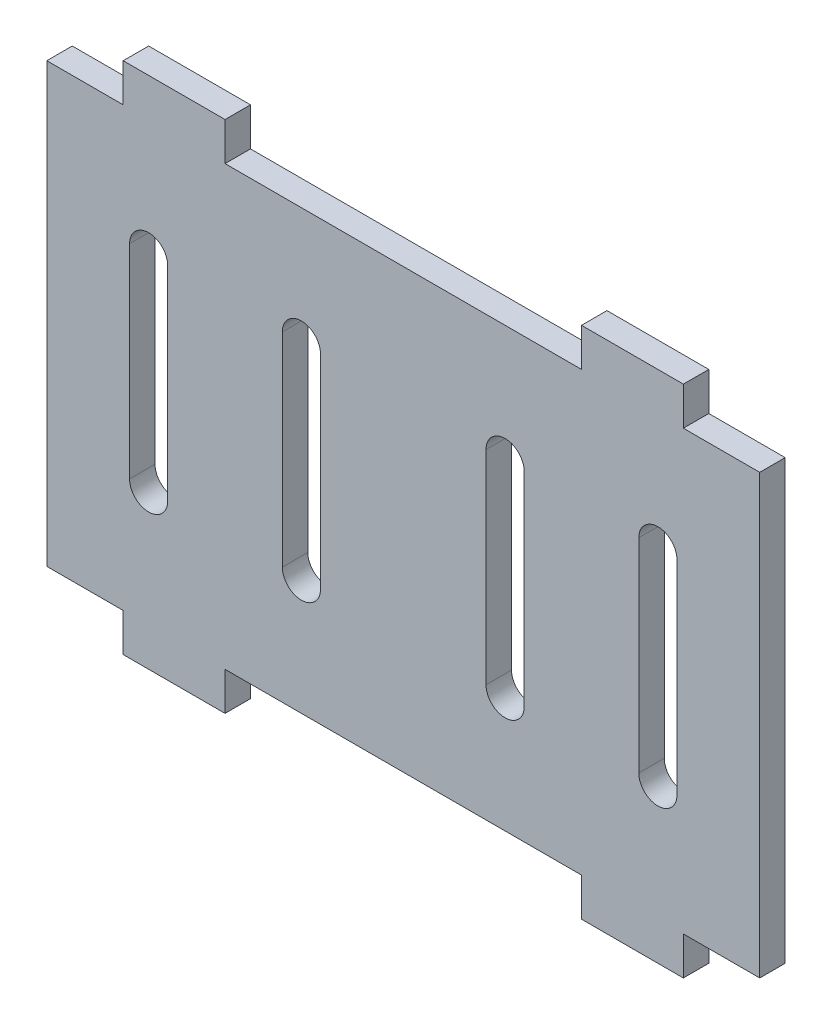
SolidWorks part; units mm, degrees
ref_plane "前视基准面" through (0, 0, 0) normal (0, 0, 1) x (1, 0, 0)
ref_plane "上视基准面" through (0, 0, 0) normal (0, 1, 0) x (1, 0, 0)
ref_plane "右视基准面" through (0, 0, 0) normal (1, 0, 0) x (0, 0, -1)
sketch "草图1" plane through (0, 0, 0) normal (0, 0, 1) x (1, 0, 0)
  line L1 (-28, 17.2) -> (28, 17.2)
  line L2 (-28, 17.2) -> (-28, -17.2)
  line L3 (-28, -17.2) -> (28, -17.2)
  line L4 (28, 17.2) -> (28, -17.2)
  dimension "D1" = 34.4
  dimension "D2" = 56
extrude "凸台-拉伸1" add sketch "草图1" along normal blind 2
sketch "草图2" plane through (0, -17.2, 0) normal (0, -1, 0) x (1, 0, 0)
  line L0 (-28, 0) -> (28, 0) construction
  line L1 (-14, 0) -> (-22, 0)
  line L2 (-14, 0) -> (-14, 2)
  line L3 (-14, 2) -> (-22, 2)
  line L4 (-22, 0) -> (-22, 2)
  dimension "D1" = 8
  dimension "D2" = 14
  dimension "D3" = 2
extrude "凸台-拉伸2" add sketch "草图2" along normal blind 6
mirror "镜向1" about plane through (0, 0, 0) normal (0, 1, 0) of "凸台-拉伸2"
mirror "镜向2" about plane through (0, 0, 0) normal (1, 0, 0) of "镜向1", "凸台-拉伸2"
sketch "草图4" plane through (-14, 0, 0) normal (1, 0, 0) x (0, 0, -1)
  line L0 (-2, -23.2) -> (-2, -21.7)
  line L1 (-2, -23.2) -> (0, -23.2) construction
  line L2 (-2, -23.2) -> (-2, -17.2) construction
  line L3 (-2, -21.7) -> (-3, -21.7)
  line L4 (-3, -21.7) -> (-2, -23.2)
  line L5 (0, -23.2) -> (0, -17.2) construction
  line L6 (-6, -21.2) -> (46, -21.2) construction
  dimension "D1" = 3
  dimension "D2" = 1.5
  dimension "D3" = 0.5
extrude "凸台-拉伸3" add sketch "草图4" against normal up to surface (8 mm away) contours L4 L0 L3 up to face at (-22, -20.2, 1)
sketch "草图5" plane through (22, 0, 0) normal (1, 0, 0) x (0, 0, -1)
  line L0 (-2, -21.7) -> (-3, -21.7) construction
  line L1 (-3, -21.7) -> (-2, -23.2) construction
  line L2 (-2, -21.7) -> (-3, -21.7)
  line L3 (-3, -21.7) -> (-2, -23.2)
  line L4 (-2, -23.2) -> (-2, -21.7)
  line L5 (0, 0) -> (-13.4188, 0) construction
  line L6 (-2, 23.2) -> (-2, 21.7)
  line L7 (-3, 21.7) -> (-2, 23.2)
  line L8 (-2, 21.7) -> (-3, 21.7)
extrude "凸台-拉伸4" add sketch "草图5" against normal up to surface (8 mm away) up to face at (14, -20.2, 1)
sketch "草图6" plane through (-14, 0, 0) normal (1, 0, 0) x (0, 0, -1)
  line L2 (-2, 23.2) -> (-2, 21.7)
  line L3 (-2, 21.7) -> (-3, 21.7)
  line L4 (-3, 21.7) -> (-2, 23.2)
extrude "凸台-拉伸5" add sketch "草图6" against normal up to surface (8 mm away) up to face at (-22, 20.2, 1)
sketch "草图7" plane through (0, 0, 2) normal (0, 0, 1) x (1, 0, 0)
  line L0 (-8, -8) -> (-8, 8) construction
  line L13 (-9.5, -8) -> (-9.5, 8)
  line L14 (-6.5, -8) -> (-6.5, 8)
  line L15 (-20, -8) -> (-20, 8) construction
  line L16 (-21.5, -8) -> (-21.5, 8)
  line L17 (-18.5, -8) -> (-18.5, 8)
  line L18 (8, -8) -> (8, 8) construction
  line L19 (6.5, -8) -> (6.5, 8)
  line L20 (9.5, -8) -> (9.5, 8)
  line L21 (20, -8) -> (20, 8) construction
  line L24 (0, 0) -> (0, -27.6306) construction
  line L25 (0, 0) -> (-39.4623, 0) construction
  line L26 (21.5, -8) -> (21.5, 8)
  line L27 (18.5, -8) -> (18.5, 8)
  arc A4 (-9.5, -8) -> (-6.5, -8) centre (-8, -8) ccw
  arc A5 (-6.5, 8) -> (-9.5, 8) centre (-8, 8) ccw
  arc A6 (-21.5, -8) -> (-18.5, -8) centre (-20, -8) ccw
  arc A7 (-18.5, 8) -> (-21.5, 8) centre (-20, 8) ccw
  arc A8 (6.5, -8) -> (9.5, -8) centre (8, -8) ccw
  arc A9 (9.5, 8) -> (6.5, 8) centre (8, 8) ccw
  arc A12 (21.5, -8) -> (18.5, -8) centre (20, -8) cw
  arc A13 (18.5, 8) -> (21.5, 8) centre (20, 8) cw
  point P2 (-20, 0)
  point P7 (8, 0)
  point P10 (-8, 0)
  point P23 (20, 0)
  dimension "D1" = 1.5
  dimension "D2" = 16
  dimension "D3" = 40
  dimension "D4" = 16
extrude "切除-拉伸1" cut sketch "草图7" against normal blind 10
sketch "草图8" plane through (0, 0, 2) normal (0, 0, 1) x (1, 0, 0)
  line L0 (0, 0) -> (79.2167, 0) construction
  line L1 (-30.3424, 35.4823) -> (39.6119, 35.4823)
  line L2 (-30.3424, 35.4823) -> (-30.3424, 20.2)
  line L3 (-30.3424, 20.2) -> (39.6119, 20.2)
  line L4 (39.6119, 35.4823) -> (39.6119, 20.2)
  line L5 (37.2442, -20.2) -> (-37.8759, -20.2)
  line L6 (37.2442, -20.2) -> (37.2442, -27.303)
  line L7 (37.2442, -27.303) -> (-37.8759, -27.303)
  line L8 (-37.8759, -20.2) -> (-37.8759, -27.303)
  line L9 (28, 17.2) -> (22, 17.2) construction
  dimension "D1" = 3
extrude "切除-拉伸3" cut sketch "草图8" against normal through all both and the other way through all
